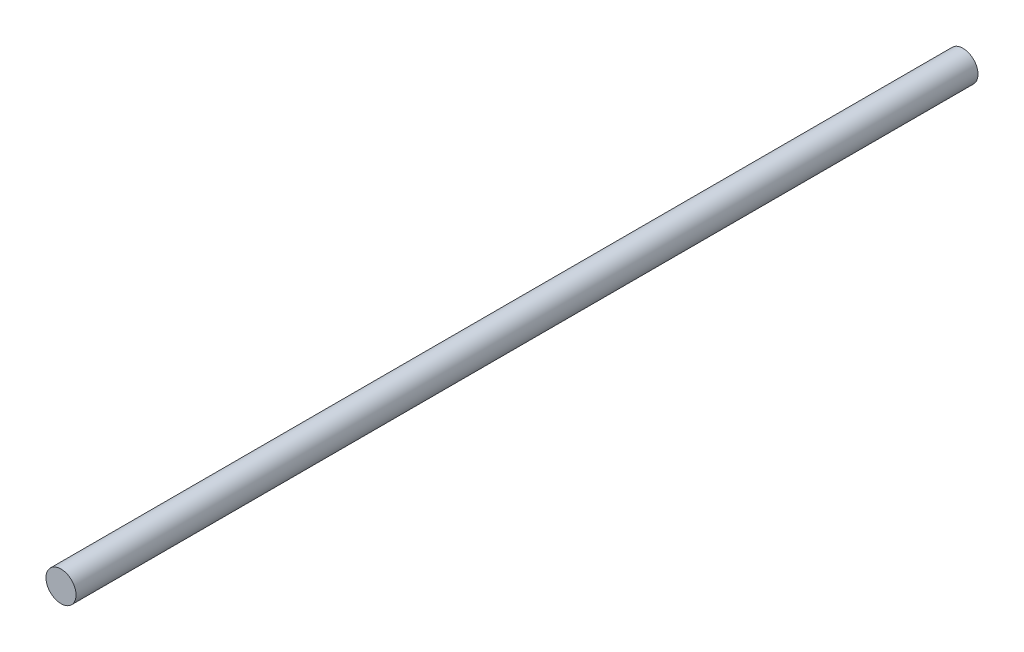
SolidWorks part; units mm, degrees
ref_plane "Front Plane" through (0, 0, 0) normal (0, 0, 1) x (1, 0, 0)
ref_plane "Top Plane" through (0, 0, 0) normal (0, 1, 0) x (1, 0, 0)
ref_plane "Right Plane" through (0, 0, 0) normal (1, 0, 0) x (0, 0, -1)
sketch "Sketch1" plane through (0, 0, 0) normal (0, 0, 1) x (1, 0, 0)
  circle A0 centre (0, 0) radius 6.35
extrude "Boss-Extrude1" add sketch "Sketch1" along normal blind 381
